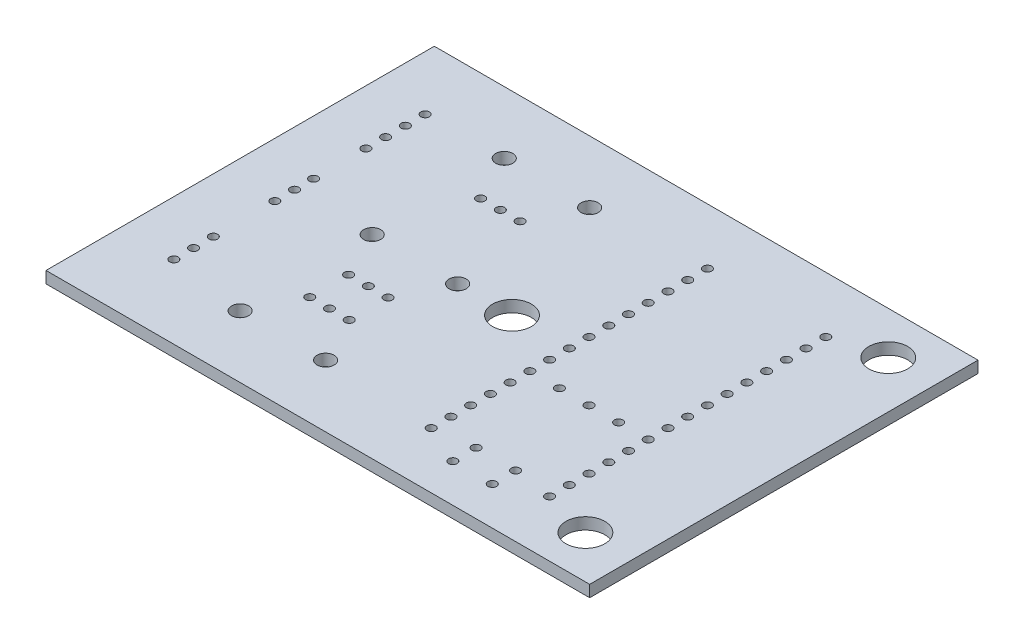
SolidWorks part; units mm, degrees
ref_plane "Front Plane" through (0, 0, 0) normal (0, 0, 1) x (1, 0, 0)
ref_plane "Top Plane" through (0, 0, 0) normal (0, 1, 0) x (1, 0, 0)
ref_plane "Right Plane" through (0, 0, 0) normal (1, 0, 0) x (0, 0, -1)
sketch "Sketch1" plane through (0, 0, 0) normal (0, 1, 0) x (1, 0, 0)
  line L1 (-35, -25) -> (35, -25)
  line L2 (-35, -25) -> (-35, 25)
  line L3 (-35, 25) -> (35, 25)
  line L4 (35, -25) -> (35, 25)
  line L5 (-35, -25) -> (35, 25) construction
  line L6 (-35, 25) -> (35, -25) construction
  point P0 (0, 0)
  dimension "D1" = 70
  dimension "D2" = 50
extrude "Boss-Extrude1" add sketch "Sketch1" along normal blind 1.5
sketch "Sketch2" plane through (0, 1.5, 0) normal (0, 1, 0) x (1, 0, 0)
  circle A1 centre (28.95, -19.5) radius 2 construction
  circle A2 centre (0, 0) radius 2.5
  circle A5 centre (28.95, -19.5) radius 2 construction
  circle A8 centre (28.95, 19.5) radius 2 construction
  circle A9 centre (28.95, 19.5) radius 2 construction
  circle A11 centre (28.95, 19.5) radius 2.5
  circle A12 centre (28.95, -19.5) radius 2.5
  circle A14 centre (0, 0) radius 2.5 construction
  dimension "D1" = 0.5
extrude "Cut-Extrude1" cut sketch "Sketch2" against normal through all
sketch "Sketch3" plane through (0, 1.5, 0) normal (0, 1, 0) x (1, 0, 0)
  line L1 (5.5, -23) -> (24.5, -23)
  line L2 (5.5, -23) -> (5.5, 23)
  line L3 (5.5, 23) -> (24.5, 23)
  line L4 (24.5, -23) -> (24.5, 23)
  line L5 (5.5, -23) -> (24.5, 23) construction
  line L6 (5.5, 23) -> (24.5, -23) construction
  line L7 (-6.5, -23) -> (-18.5, -23)
  line L8 (-6.5, -23) -> (-6.5, 23)
  line L9 (-6.5, 23) -> (-18.5, 23)
  line L10 (-18.5, -23) -> (-18.5, 23)
  line L11 (-6.5, -23) -> (-18.5, 23) construction
  line L12 (-6.5, 23) -> (-18.5, -23) construction
  line L13 (-24, -21) -> (-32, -21)
  line L14 (-24, -21) -> (-24, 21)
  line L15 (-24, 21) -> (-32, 21)
  line L16 (-32, -21) -> (-32, 21)
  line L17 (-24, -21) -> (-32, 21) construction
  line L18 (-24, 21) -> (-32, -21) construction
  point P0 (15, 0)
  point P5 (-28, 0)
  point P14 (-12.5, 0)
  dimension "D1" = 19
  dimension "D2" = 46
  dimension "D3" = 12.5
  dimension "D4" = 15
  dimension "D5" = 28
  dimension "D6" = 46
  dimension "D7" = 42
  dimension "D8" = 8
  dimension "D9" = 12
sketch "Sketch4" plane through (0, 1.5, 0) normal (0, 1, 0) x (1, 0, 0)
  line L0 (-12.5, 24) -> (-12.5, -24) construction
  line L1 (7.38, 0) -> (22.62, 0) construction
  line L4 (15, -24) -> (15, 24) construction
  line L5 (-18, -6) -> (-7, -6) construction
  line L6 (-33, 0) -> (-23, 0) construction
  line L7 (-18, -6) -> (-18, 6) construction
  line L12 (-18, 6) -> (-7, 6) construction
  line L18 (-7, -6) -> (-7, 6) construction
  line L24 (-18, -6) -> (-7, 6) construction
  line L26 (-18, 6) -> (-7, -6) construction
  line L27 (-18, 11) -> (-7, 11) construction
  line L28 (-18, 11) -> (-18, 23) construction
  line L29 (-18, 23) -> (-7, 23) construction
  line L30 (-7, 11) -> (-7, 23) construction
  line L31 (-18, 11) -> (-7, 23) construction
  line L32 (-18, 23) -> (-7, 11) construction
  line L33 (-18, -23) -> (-7, -23) construction
  line L34 (-18, -23) -> (-18, -11) construction
  line L35 (-18, -11) -> (-7, -11) construction
  line L36 (-7, -23) -> (-7, -11) construction
  line L37 (-18, -23) -> (-7, -11) construction
  line L38 (-18, -11) -> (-7, -23) construction
  line L42 (6.5, -22) -> (23.5, -22) construction
  line L43 (6.5, -22) -> (6.5, 22) construction
  line L44 (6.5, 22) -> (23.5, 22) construction
  line L45 (23.5, -22) -> (23.5, 22) construction
  line L46 (6.5, -22) -> (23.5, 22) construction
  line L47 (6.5, 22) -> (23.5, -22) construction
  line L49 (-28, 9.19) -> (-28, 11.73) construction
  line L50 (-28, 11.73) -> (-28, 14.27) construction
  line L51 (7.38, -17.78) -> (7.38, -20.32) construction
  line L52 (-28, -10.46) -> (-28, -13) construction
  line L53 (-28, -13) -> (-28, -15.54) construction
  line L54 (22.62, -17.78) -> (22.62, -20.32) construction
  line L55 (28.95, 19.5) -> (28.95, 7.5) construction
  line L56 (-28, 14.27) -> (-28, 16.81) construction
  line L57 (-18, -17) -> (-7, -17) construction
  line L58 (7.38, -5.08) -> (11.19, -5.08) construction
  line L59 (11.19, -5.08) -> (15, -5.08) construction
  line L60 (15, -5.08) -> (18.81, -5.08) construction
  line L61 (18.81, -5.08) -> (22.62, -5.08) construction
  line L62 (7.38, -17.78) -> (8.1305, -17.78) construction
  line L63 (7.38, -17.78) -> (7.38, -25) construction
  line L64 (21.8695, -17.78) -> (22.62, -17.78) construction
  line L65 (-35, -25) -> (35, -25) construction
  line L66 (22.62, -17.78) -> (22.62, -25) construction
  line L67 (12.46, -20.08) -> (17.54, -20.08) construction
  line L68 (17.54, -20.08) -> (22.62, -20.08) construction
  line L69 (12.46, -20.08) -> (7.38, -20.08) construction
  line L70 (-33, -10) -> (-33, 10) construction
  line L71 (-23, 10) -> (-23, -10) construction
  line L72 (-19.5, -24) -> (-5.5, -24) construction
  line L73 (-5.5, 24) -> (-19.5, 24) construction
  line L74 (25.5, 24) -> (4.5, 24) construction
  circle A0 centre (-18, 0) radius 1.1
  circle A1 centre (-7, 0) radius 1.1
  circle A2 centre (-12.5, -6) radius 0.55
  circle A3 centre (-9.96, -6) radius 0.55
  circle A4 centre (-15.04, -6) radius 0.55
  circle A5 centre (-12.5, 11) radius 0.55
  circle A6 centre (-9.96, 11) radius 0.55
  circle A7 centre (-15.04, 11) radius 0.55
  circle A8 centre (-18, 17) radius 1.1
  circle A9 centre (-7, 17) radius 1.1
  circle A10 centre (-12.5, -23) radius 0.55 construction
  circle A11 centre (-9.96, -23) radius 0.55 construction
  circle A12 centre (-15.04, -23) radius 0.55 construction
  circle A13 centre (-18, -17) radius 1.1
  circle A14 centre (-7, -17) radius 1.1
  circle A15 centre (7.38, 0) radius 0.55
  circle A16 centre (22.62, 0) radius 0.55
  circle A17 centre (7.38, 2.54) radius 0.55
  circle A18 centre (7.38, 5.08) radius 0.55
  circle A19 centre (7.38, 7.62) radius 0.55
  circle A20 centre (7.38, 10.16) radius 0.55
  circle A21 centre (7.38, 12.7) radius 0.55
  circle A22 centre (7.38, 15.24) radius 0.55
  circle A23 centre (7.38, 17.78) radius 0.55
  circle A24 centre (22.62, 2.54) radius 0.55
  circle A25 centre (22.62, 5.08) radius 0.55
  circle A26 centre (22.62, 7.62) radius 0.55
  circle A27 centre (22.62, 10.16) radius 0.55
  circle A28 centre (22.62, 12.7) radius 0.55
  circle A29 centre (22.62, 15.24) radius 0.55
  circle A30 centre (22.62, 17.78) radius 0.55
  circle A31 centre (22.62, -17.78) radius 0.55
  circle A32 centre (22.62, -15.24) radius 0.55
  circle A33 centre (22.62, -12.7) radius 0.55
  circle A34 centre (22.62, -10.16) radius 0.55
  circle A35 centre (22.62, -7.62) radius 0.55
  circle A36 centre (22.62, -5.08) radius 0.55
  circle A37 centre (22.62, -2.54) radius 0.55
  circle A38 centre (7.38, -17.78) radius 0.55
  circle A39 centre (7.38, -15.24) radius 0.55
  circle A40 centre (7.38, -12.7) radius 0.55
  circle A41 centre (7.38, -10.16) radius 0.55
  circle A42 centre (7.38, -7.62) radius 0.55
  circle A43 centre (7.38, -5.08) radius 0.55
  circle A44 centre (7.38, -2.54) radius 0.55
  circle A52 centre (-28, -13) radius 0.55
  circle A53 centre (-28, -10.46) radius 0.55
  circle A54 centre (-28, -15.54) radius 0.55
  circle A55 centre (-28, 11.73) radius 0.55
  circle A56 centre (-28, 14.27) radius 0.55
  circle A57 centre (-28, 9.19) radius 0.55
  circle A58 centre (-28, 16.81) radius 0.55
  circle A59 centre (28.95, 7.5) radius 0.55 construction
  circle A60 centre (28.95, 11.5) radius 0.55 construction
  circle A61 centre (-9.96, -11) radius 0.55
  circle A62 centre (-12.5, -11) radius 0.55
  circle A63 centre (-15.04, -11) radius 0.55
  circle A65 centre (7.38, -20.32) radius 0.55 construction
  circle A66 centre (22.62, -20.32) radius 0.55 construction
  circle A70 centre (11.19, -5.08) radius 0.55
  circle A71 centre (15, -5.08) radius 0.55
  circle A72 centre (18.81, -5.08) radius 0.55
  circle A73 centre (12.46, -20.08) radius 0.55
  circle A74 centre (17.54, -20.08) radius 0.55
  circle A75 centre (17.54, -17.08) radius 0.55
  circle A76 centre (-28, 0) radius 0.55
  circle A77 centre (-28, -2.54) radius 0.55
  circle A78 centre (-28, 2.45) radius 0.55
  circle A79 centre (12.46, -17.08) radius 0.55
  point P6 (-12.5, 0)
  point P11 (-12.5, 17)
  point P16 (-12.5, -17)
  point P21 (15, 0)
  point P67 (15, 0)
  point P131 (-28, 13)
  point P134 (-28, 0)
  dimension "D11" = 2.2
  dimension "D14" = 1.1
  dimension "D16" = 1.1
  dimension "D19" = 2.54
  dimension "D23" = 1.1
  dimension "D26" = 1.1
  dimension "D1" = 11
  dimension "D2" = 12
  dimension "D3" = 12
  dimension "D4" = 11
  dimension "D5" = 12
  dimension "D6" = 11
  dimension "D7" = 5
  dimension "D8" = 5
  dimension "D9" = 44
  dimension "D10" = 17
  dimension "D12" = 2.54
  dimension "D13" = 2.54
  dimension "D15" = 15.24
  dimension "D18" = 2.54
  dimension "D20" = 13
  dimension "D21" = 2.54
  dimension "D22" = 2.54
  dimension "D24" = 2.54
  dimension "D25" = 2.54
  dimension "D27" = 4
  dimension "D28" = 12
  dimension "D29" = 13
  dimension "D30" = 2.54
  dimension "D31" = 3
  dimension "D32" = 12
  dimension "D33" = 2.45
  dimension "D34" = 2.54
  dimension "D17" = 8
extrude "Cut-Extrude2" cut sketch "Sketch4" against normal through all
sketch "Sketch5" plane through (0, 0, 0) normal (0, -1, 0) x (1, 0, 0)
  line L0 (7.38, 17.78) -> (12.46, 20.08)
  line L1 (11.19, 5.08) -> (12.46, 17.08) construction
  line L2 (17.54, 17.08) -> (17.54, 20.08)
  line L3 (7.38, 15.24) -> (12.46, 17.08)
  line L4 (15, 5.08) -> (17.54, 17.08) construction
  line L5 (18.81, 5.08) -> (17.54, 17.08) construction
  line L6 (7.38, 10.16) -> (-12.5, 14.6313)
  line L7 (-12.5, 14.6313) -> (-12.5, 11)
  line L8 (-12.5, 11) -> (-12.5, 6)
  line L9 (-12.5, 6) -> (-12.5, -11)
  line L10 (-9.96, 11) -> (7.38, 5.08)
  line L11 (-9.96, 6) -> (7.38, 2.54)
  line L12 (-9.96, -11) -> (7.38, 0)
  line L13 (-28, -11.73) -> (-15.6404, -15.2852)
  line L14 (-15.6404, -15.2852) -> (-14.4697, -19.1168)
  line L15 (7.38, 5.08) -> (11.19, 5.08)
  line L16 (-5.8801, -12.7719) -> (7.38, -5.08)
  line L17 (-28, -14.27) -> (-22.3082, -21.162)
  line L18 (7.38, 2.54) -> (15, 2.54)
  line L19 (7.38, 15.24) -> (2.9693, 15.24)
  line L20 (2.9693, 15.24) -> (2.9693, 19.5829)
  line L21 (2.9693, 19.5829) -> (-20.1603, 19.5829)
  line L22 (-20.1603, 19.5829) -> (-20.1603, 10.46)
  line L23 (-12.5, 2.5) -> (-28, 2.54)
  line L24 (-28, -9.19) -> (-28, -2.45)
  line L25 (-20.1603, 10.46) -> (-28, 10.46)
  line L26 (-23.6743, 21.3866) -> (-23.6743, 13)
  line L27 (-23.6743, 21.3866) -> (7.38, 21.3866)
  line L28 (7.38, 21.3866) -> (7.38, 17.78)
  line L29 (-32.1913, 15.54) -> (-28, 15.54)
  line L30 (-32.1913, 15.54) -> (-32.1913, 23.4922)
  line L31 (-32.1913, 23.4922) -> (25.6428, 23.4922)
  line L32 (25.6428, 23.4922) -> (25.6428, 7.62)
  line L33 (22.62, 7.62) -> (25.6428, 7.62)
  line L34 (-28, -16.81) -> (-28, -23.6469)
  line L35 (-28, -23.6469) -> (22.62, -23.6469)
  line L36 (22.62, -23.6469) -> (22.62, -17.78)
  line L37 (15, 2.54) -> (15, 5.08)
  line L38 (7.38, 0) -> (18.81, 0)
  line L39 (18.81, 0) -> (18.81, 5.08)
  line L40 (-28, -2.45) -> (-32.1913, -2.45)
  line L41 (-32.1913, -2.45) -> (-32.1913, 10.46)
  line L42 (-32.1913, 10.46) -> (-28, 10.46)
  line L43 (-22.3082, -21.162) -> (15, -21.162)
  line L44 (-14.4697, -19.1168) -> (-0.9526, -19.1168)
  line L45 (-0.9526, -19.1168) -> (7.38, -7.62)
  line L46 (-5.8801, -12.7719) -> (-16.8816, -12.7719)
  line L47 (-28, 0) -> (-23.0059, 0)
  line L48 (-23.0059, 0) -> (-16.8816, -12.7719)
  line L49 (12.46, 17.08) -> (17.54, 17.08)
  line L50 (7.38, -2.54) -> (15, -2.54)
  line L51 (15, -2.54) -> (15, -21.162)
  line L52 (-23.6743, 13) -> (-28, 13)
  point P62 (25.6428, 8.0298)
  point P67 (-28, 0)
  point P80 (-28, 2.54)
  point P81 (-28, -2.45)
